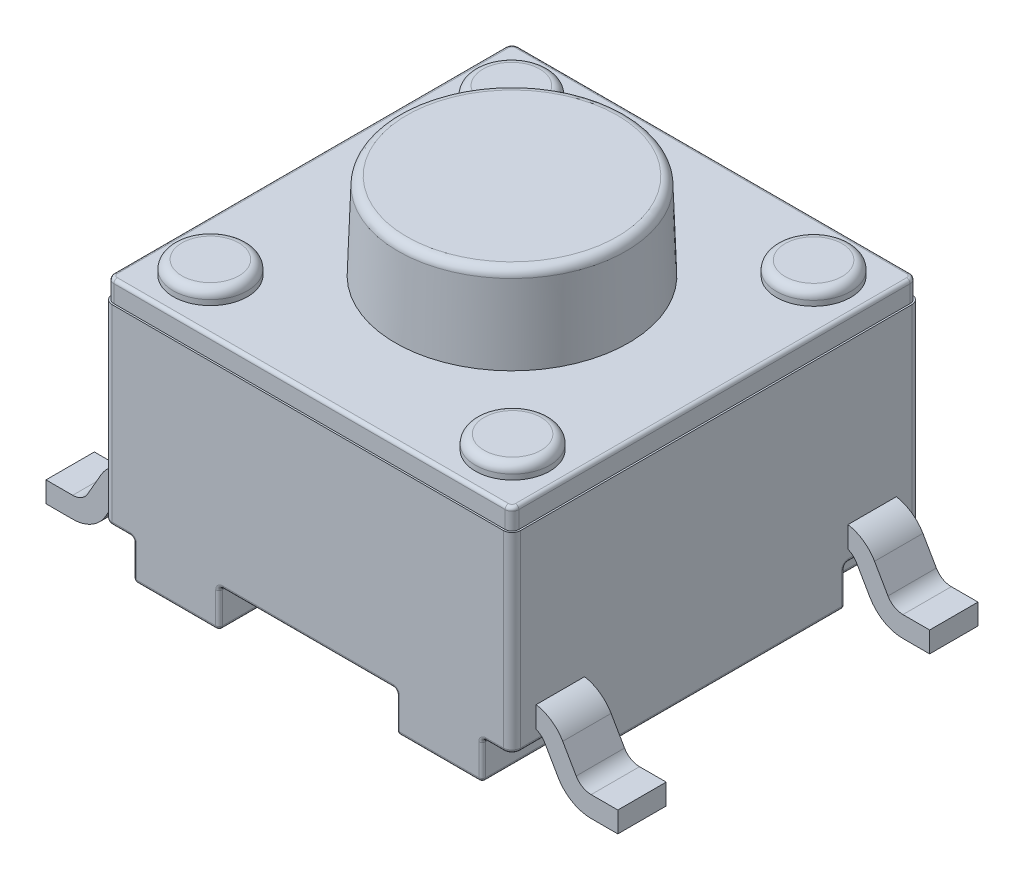
SolidWorks part; units mm, degrees
ref_plane "Front Plane" through (0, 0, 0) normal (0, 0, 1) x (1, 0, 0)
ref_plane "Top Plane" through (0, 0, 0) normal (0, 1, 0) x (1, 0, 0)
ref_plane "Right Plane" through (0, 0, 0) normal (1, 0, 0) x (0, 0, -1)
sketch "Sketch1" plane through (0, 0, 0) normal (0, 1, 0) x (1, 0, 0)
  line L1 (-3.0035, -3.0035) -> (3.0035, -3.0035)
  line L2 (-3.0035, -3.0035) -> (-3.0035, 3.0036)
  line L3 (-3.0035, 3.0036) -> (3.0035, 3.0036)
  line L4 (3.0035, -3.0035) -> (3.0035, 3.0036)
  line L5 (-3.0035, -3.0035) -> (3.0035, 3.0036) construction
  line L6 (-3.0035, 3.0036) -> (3.0035, -3.0035) construction
  point P0 (0, 0)
  dimension "D1" = 6.0071
  dimension "D2" = 6.0071
extrude "Boss-Extrude1" add sketch "Sketch1" along normal blind 2.8194 from offset 0.5588
fillet "Fillet1" radius 0.127 4 edges at (-3.0035, 1.9685, 3.0035) (-3.0035, 1.9685, -3.0036) (3.0035, 1.9685, -3.0036) (3.0035, 1.9685, 3.0035)
sketch "Sketch2" plane through (0, 3.3782, 0) normal (0, -1, 0) x (-1, 0, 0)
  line L8 (2.9781, -2.8765) -> (2.9781, 2.8765)
  line L9 (-2.8765, -2.9781) -> (2.8765, -2.9781)
  line L10 (-2.9781, 2.8765) -> (-2.9781, -2.8765)
  line L11 (2.8765, 2.9782) -> (-2.8765, 2.9782)
  line L12 (2.9781, -2.8765) -> (2.9781, 2.8765)
  line L13 (-2.8765, -2.9781) -> (2.8765, -2.9781)
  line L14 (-2.9781, 2.8765) -> (-2.9781, -2.8765)
  line L15 (2.8765, 2.9782) -> (-2.8765, 2.9782)
  arc A8 (2.8765, -2.9781) -> (2.9781, -2.8765) centre (2.8765, -2.8765) ccw
  arc A9 (-2.9781, -2.8765) -> (-2.8765, -2.9781) centre (-2.8765, -2.8765) ccw
  arc A10 (-2.8765, 2.9782) -> (-2.9781, 2.8765) centre (-2.8765, 2.8766) ccw
  arc A11 (2.9781, 2.8765) -> (2.8765, 2.9782) centre (2.8765, 2.8765) ccw
  arc A12 (2.8765, -2.9781) -> (2.9781, -2.8765) centre (2.8765, -2.8765) ccw
  arc A13 (-2.9781, -2.8765) -> (-2.8765, -2.9781) centre (-2.8765, -2.8765) ccw
  arc A14 (-2.8765, 2.9782) -> (-2.9781, 2.8765) centre (-2.8765, 2.8766) ccw
  arc A15 (2.9781, 2.8765) -> (2.8765, 2.9782) centre (2.8765, 2.8765) ccw
  dimension "D1" = 0.0254
extrude "Boss-Extrude2" add sketch "Sketch2" against normal blind 0.3048
sketch "Sketch3" plane through (0, 0, 0) normal (0, 1, 0) x (1, 0, 0)
  line L0 (-2.5662, -3.0035) -> (-2.5662, -1.8948)
  line L1 (-2.8765, -3.0035) -> (2.8765, -3.0035) construction
  line L2 (-2.5662, -1.8948) -> (-3.0035, -1.8948)
  line L3 (-3.0035, 2.8765) -> (-3.0035, -2.8765) construction
  line L4 (-2.4413, -0.5609) -> (-1.3018, -0.5609)
  line L5 (-1.3018, -0.5609) -> (-1.3017, -3.0035)
  line L6 (-2.4413, -0.5609) -> (-2.4413, 0.5609)
  line L7 (-2.5662, -3.0035) -> (-1.3017, -3.0035)
  line L8 (-3.0035, -1.8948) -> (-3.0035, 1.8948)
  line L9 (-2.4413, 0) -> (-3.0035, 0) construction
  line L10 (-2.5662, 3.0036) -> (-1.3017, 3.0035)
  line L11 (-1.3017, 0.5609) -> (-1.3017, 3.0035)
  line L12 (-2.4413, 0.5609) -> (-1.3017, 0.5609)
  line L13 (-2.5662, 1.8948) -> (-3.0035, 1.8948)
  line L14 (-2.5662, 3.0036) -> (-2.5662, 1.8948)
  line L15 (0, -3.0035) -> (0, 3.0036) construction
  line L16 (2.8765, 3.0036) -> (-2.8765, 3.0036) construction
  line L17 (2.4413, 0) -> (3.0035, 0) construction
  line L18 (2.5662, 3.0035) -> (2.5662, 1.8948)
  line L19 (2.5662, 1.8948) -> (3.0035, 1.8948)
  line L20 (2.4413, 0.5609) -> (1.3017, 0.5609)
  line L21 (1.3017, 0.5609) -> (1.3017, 3.0035)
  line L22 (2.5662, 3.0035) -> (1.3017, 3.0035)
  line L23 (3.0035, -1.8948) -> (3.0035, 1.8948)
  line L24 (2.5662, -3.0036) -> (1.3017, -3.0036)
  line L25 (2.4413, -0.5609) -> (2.4413, 0.5609)
  line L26 (1.3017, -0.5609) -> (1.3017, -3.0036)
  line L27 (2.4413, -0.5609) -> (1.3017, -0.5609)
  line L28 (2.5662, -1.8948) -> (3.0035, -1.8948)
  line L29 (2.5662, -3.0036) -> (2.5662, -1.8948)
  dimension "D1" = 1.7018
extrude "Boss-Extrude3" add sketch "Sketch3" along normal up to next
sketch "Sketch4" plane through (0, 3.683, 0) normal (0, 1, 0) x (1, 0, 0)
  line L1 (-2.2217, -2.2129) -> (2.2217, -2.2129) construction
  line L2 (-2.2217, -2.2129) -> (-2.2217, 2.2129) construction
  line L3 (-2.2217, 2.2129) -> (2.2217, 2.2129) construction
  line L4 (2.2217, -2.2129) -> (2.2217, 2.2129) construction
  line L5 (-2.2217, -2.2129) -> (2.2217, 2.2129) construction
  line L6 (-2.2217, 2.2129) -> (2.2217, -2.2129) construction
  circle A0 centre (2.2217, 2.2129) radius 0.5461
  circle A1 centre (-2.2217, 2.2129) radius 0.5461
  circle A2 centre (-2.2217, -2.2129) radius 0.5461
  circle A3 centre (2.2217, -2.2129) radius 0.5461
  point P0 (0, 0)
  dimension "D1" = 1.0922
extrude "Boss-Extrude4" add sketch "Sketch4" along normal blind 0.2032
sketch "Sketch5" plane through (0, 3.683, 0) normal (0, 1, 0) x (1, 0, 0)
  circle A0 centre (0, 0) radius 1.7145
  dimension "D1" = 3.429
extrude "Boss-Extrude5" add sketch "Sketch5" along normal blind 1.27 draft 2
fillet "Fillet2" radius 0.127 5 edges at (-2.2217, 3.8862, -1.6668) (-2.2217, 3.8862, 2.759) (2.2217, 3.8862, -1.6668) (2.2217, 3.8862, 2.759) (0, 4.953, 1.6702)
fillet "Fillet3" radius 0.0508 88 edges at (2.9664, 0.5588, 2.9664) (2.9664, 0.5588, -2.9664) (-2.9664, 0.5588, -2.9664) (-2.9664, 0.5588, 2.9664) (3.0035, 0.5588, 2.3857) (3.0035, 0.5588, -2.3857) (1.3017, 0.2794, 3.0036) (1.3017, 0.2794, -3.0035) (2.9484, 3.683, -2.9484) (0, 3.683, -2.9782) (-2.9484, 3.683, -2.9484) (-2.9781, 3.683, 0) (-2.9484, 3.683, 2.9484) (0, 3.683, 2.9781) (2.9484, 3.683, 2.9484) (2.4413, 0.2794, 0.5609) (1.3017, 0.2794, 0.5609) (1.3017, 0.2794, -0.5609) (2.4413, 0.2794, -0.5609) (-1.3018, 0.2794, 0.5609) (-2.4413, 0.2794, 0.5609) (-2.4413, 0.2794, -0.5609) (-1.3017, 0.2794, -0.5609) (2.7849, 0.5588, 1.8948) (3.0035, 0.2794, 1.8948) (2.5662, 0.2794, 3.0036) (2.5662, 0.5588, 2.4492) (2.5662, 0.2794, 1.8948) (3.0035, 0.2794, -1.8948) (2.7849, 0.5588, -1.8948) (2.5662, 0.2794, -1.8948) (2.5662, 0.5588, -2.4492) (2.5662, 0.2794, -3.0035) (-2.5662, 0.2794, -1.8948) (-2.5662, 0.2794, 1.8948) (-1.8715, 0.5588, -0.5609) (-2.4413, 0.5588, 0) (-1.8715, 0.5588, 0.5609) (1.3017, 0.5588, 1.7822) (1.8715, 0.5588, 0.5609) (2.4413, 0.5588, 0) (1.8715, 0.5588, -0.5609) (1.3017, 0.5588, -1.7822) (-1.3017, 0, 1.7822) (-1.8715, 0, 0.5609) (-2.4413, 0, 0) (-1.8715, 0, -0.5609) (-1.3017, 0, -1.7822) (-1.934, 0, -3.0035) (-2.5662, 0, -2.4492) (-2.7849, 0, -1.8948) (-3.0035, 0, 0) (-2.7849, 0, 1.8948) (-2.5662, 0, 2.4492) (-1.934, 0, 3.0035) (1.3017, 0, -1.7822) (1.8715, 0, -0.5609) (2.4413, 0, 0) (1.8715, 0, 0.5609) (1.3017, 0, 1.7822) (1.934, 0, 3.0036) (2.5662, 0, 2.4492) (2.7849, 0, 1.8948) (3.0035, 0, 0) (2.7849, 0, -1.8948) (2.5662, 0, -2.4492) (1.934, 0, -3.0035) (2.9781, 3.683, 0)
sketch "Sketch6" plane through (0, 0, 3.0035) normal (0, 0, 1) x (1, 0, 0)
  line L0 (-3.0568, 0.7495) -> (-3.4888, 0)
  line L1 (-3.4888, 0) -> (-4.2041, 0)
  line L4 (-3.0568, 0.7495) -> (-2.5265, 0.7495)
  dimension "D1" = 3.0226
extrude "Extrude-Thin1" add sketch "Sketch6" against normal blind 0.7112 from offset 0.3556 thin offset against normal yes
mirror "Mirror1" about plane through (0, 0, 0) normal (0, 0, 1) of "Extrude-Thin1"
mirror "Mirror3" about plane through (0, 0, 0) normal (1, 0, 0) of "Mirror1", "Extrude-Thin1"
